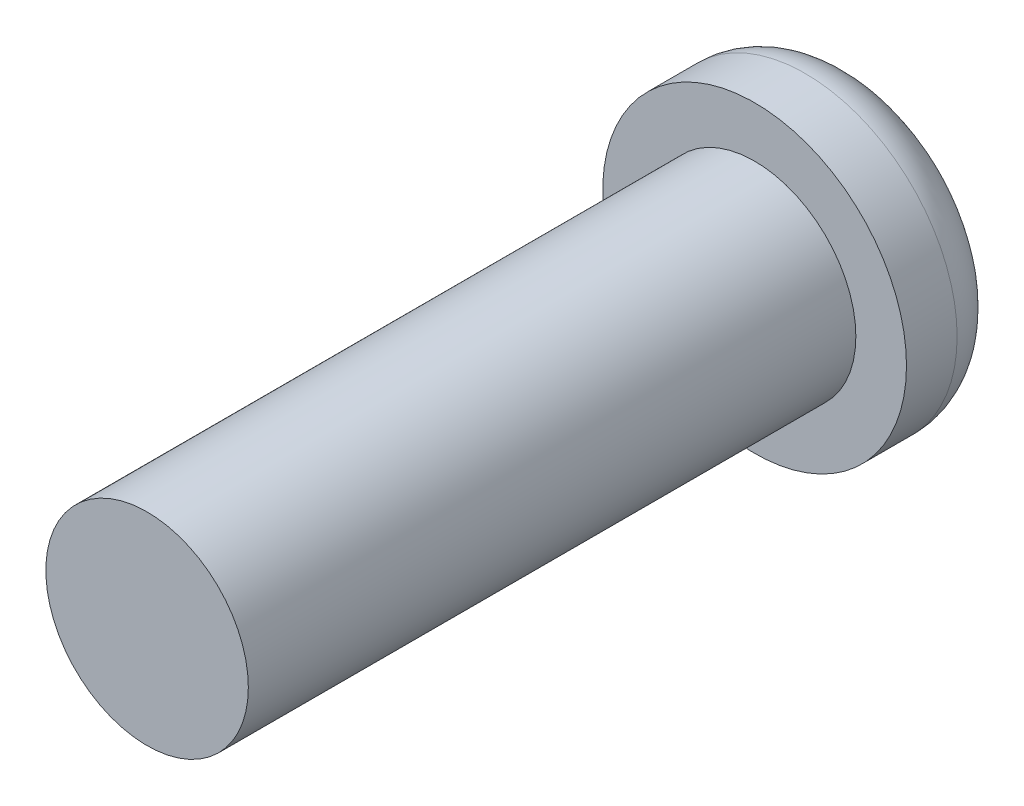
SolidWorks part; units mm, degrees
ref_plane "Front Plane" through (0, 0, 0) normal (0, 0, 1) x (1, 0, 0)
ref_plane "Top Plane" through (0, 0, 0) normal (0, 1, 0) x (1, 0, 0)
ref_plane "Right Plane" through (0, 0, 0) normal (1, 0, 0) x (0, 0, -1)
sketch "Sketch1" plane through (0, 0, 0) normal (0, 0, 1) x (1, 0, 0)
  circle A0 centre (0, 0) radius 1.5
  dimension "D1" = 3
extrude "Boss-Extrude1" add sketch "Sketch1" along normal blind 1
sketch "Sketch2" plane through (0, 0, 1) normal (0, 0, 1) x (1, 0, 0)
  circle A0 centre (0, 0) radius 1
  dimension "D1" = 2
extrude "Boss-Extrude2" add sketch "Sketch2" along normal blind 6
sketch "Sketch3" plane through (0, 0, 0) normal (0, 0, -1) x (-1, 0, 0)
  line L1 (0.2615, -0.5147) -> (0.5765, -0.0309)
  line L2 (0.5765, -0.0309) -> (0.315, 0.4838)
  line L3 (0.315, 0.4838) -> (-0.2615, 0.5147)
  line L4 (-0.2615, 0.5147) -> (-0.5765, 0.0309)
  line L5 (-0.5765, 0.0309) -> (-0.315, -0.4838)
  line L6 (-0.315, -0.4838) -> (0.2615, -0.5147)
  circle A0 centre (0, 0) radius 0.5 construction
  dimension "D1" = 1
extrude "Cut-Extrude1" cut sketch "Sketch3" against normal blind 0.75
fillet "Fillet1" radius 0.5 1 edges at (1.5, 0, 0)
